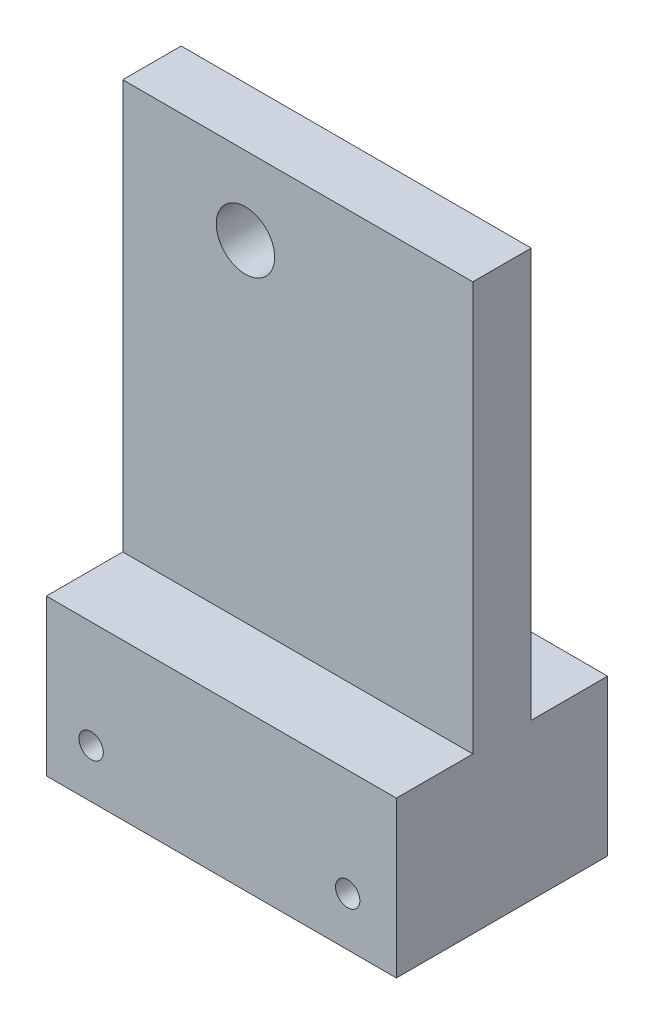
SolidWorks part; units mm, degrees
ref_plane "Ebene vorne" through (0, 0, 0) normal (0, 0, 1) x (1, 0, 0)
ref_plane "Ebene oben" through (0, 0, 0) normal (0, 1, 0) x (1, 0, 0)
ref_plane "Ebene rechts" through (0, 0, 0) normal (1, 0, 0) x (0, 0, -1)
sketch "Side" plane through (0, 0, 0) normal (0, 0, 1) x (1, 0, 0)
  line L1 (-12.6, 630) -> (23.35, 630)
  line L2 (-12.6, 630) -> (-12.6, 620)
  line L3 (-12.6, 620) -> (23.35, 620)
  line L4 (23.35, 630) -> (23.35, 620)
  line L5 (-12.6, 625) -> (23.35, 625) construction
  circle A0 centre (18.35, 625) radius 1.25
  circle A1 centre (-8, 625) radius 1.25
sketch "Skizze3" plane through (0, 0, 0) normal (0, 1, 0) x (1, 0, 0)
  line L1 (-12.6, 12.65) -> (25.15, 12.65)
  line L2 (25.15, 12.65) -> (25.15, -12.65)
  line L3 (25.15, -12.65) -> (-12.6, -12.65)
  line L5 (-12.6, 10.85) -> (23.35, 10.85)
  line L6 (23.35, 10.85) -> (23.35, -10.85)
  line L7 (23.35, -10.85) -> (-12.6, -10.85)
  arc A0 (-12.6, 12.65) -> (-12.6, -12.65) centre (-12.6, 0) ccw
  arc A1 (-12.6, 10.85) -> (-12.6, -10.85) centre (-12.6, 0) ccw
extrude "Aufsatz-Linear austragen1" add sketch "Side" along normal up to vertex (10.85 mm away) and the other way up to vertex (10.85 mm away) up to point (23.35, 0, 10.85) other way up to point (23.35, 0, -10.85)
sketch "Skizze5" plane through (0, 0, 0) normal (0, 0, 1) x (1, 0, 0)
  circle A0 centre (-8, 625) radius 1.25
  circle A1 centre (18.35, 625) radius 1.25
extrude "Schnitt-Linear austragen1" cut sketch "Skizze5" against normal through all both and the other way through all
sketch "Width" plane through (0, 0, 0) normal (1, 0, 0) x (0, 0, -1)
  line L0 (3, 670) -> (-3, 670)
  point P7 (0, 670)
sketch "TopExtension" plane through (0, 0, 0) normal (0, 0, 1) x (1, 0, 0)
  line L1 (-12.6, 630) -> (23.35, 630)
  line L2 (-12.6, 630) -> (-12.6, 678)
  line L3 (-12.6, 678) -> (23.35, 678)
  line L4 (23.35, 630) -> (23.35, 678)
  circle A0 centre (0, 670) radius 3
extrude "Aufsatz-Linear austragen2" add sketch "TopExtension" along normal up to vertex (3 mm away) and the other way up to vertex (3 mm away)
sketch "Skizze8" plane through (0, 0, 0) normal (0, 0, 1) x (1, 0, 0)
  line L0 (23.35, 630) -> (23.35, 678) construction
  line L1 (-12.6, 630) -> (23.35, 630)
  line L2 (-12.6, 630) -> (-12.6, 636)
  line L3 (-12.6, 636) -> (23.35, 636)
  line L4 (23.35, 630) -> (23.35, 636)
  dimension "D1" = 6
extrude "Aufsatz-Linear austragen3" add sketch "Skizze8" along normal up to surface and the other way up to surface contours L3 L4 L1 L2 up to face at (-6.75, 625, 10.85) other way up to face at (-6.75, 625, -10.85)
